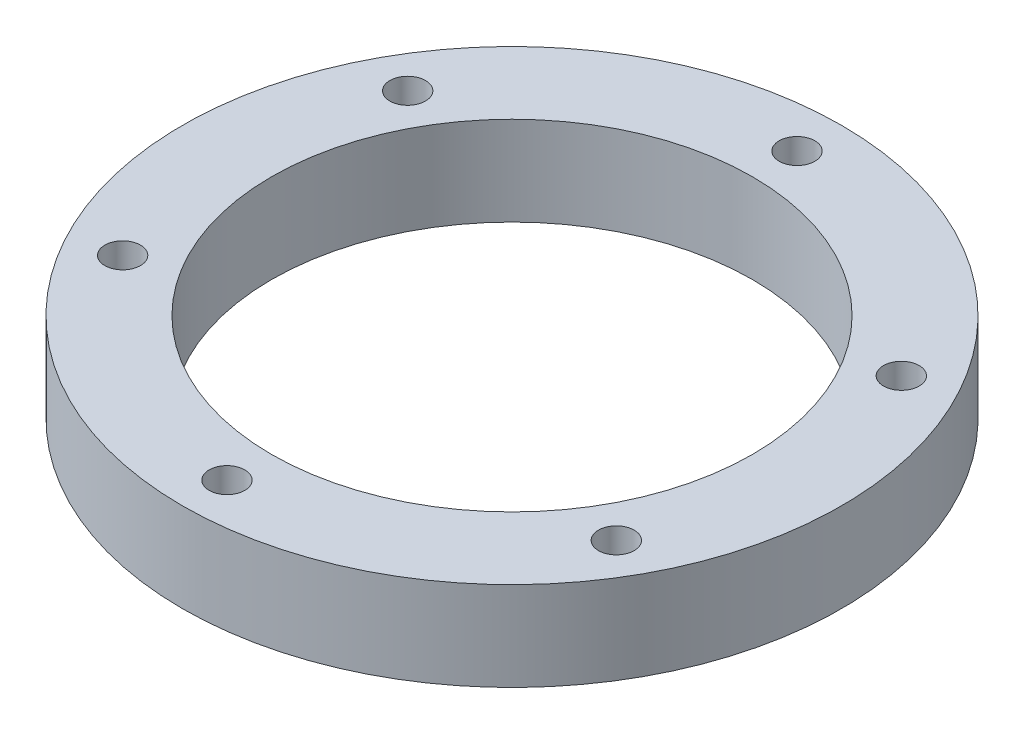
SolidWorks part; units mm, degrees
ref_plane "Front Plane" through (0, 0, 0) normal (0, 0, 1) x (1, 0, 0)
ref_plane "Top Plane" through (0, 0, 0) normal (0, 1, 0) x (1, 0, 0)
ref_plane "Right Plane" through (0, 0, 0) normal (1, 0, 0) x (0, 0, -1)
sketch "Sketch1" plane through (0, 0, 0) normal (0, 1, 0) x (1, 0, 0)
  circle A0 centre (0, 0) radius 45
extrude "Boss-Extrude1" add sketch "Sketch1" along normal blind 10
sketch "Sketch2" plane through (0, 10, 0) normal (0, 1, 0) x (1, 0, 0)
  circle A0 centre (0, 0) radius 37
  circle A1 centre (0, 0) radius 45
  circle A2 centre (0, 0) radius 27
  circle M2 centre (0, 0) radius 45
  dimension "D1" = 10
  dimension "D2" = 90
  dimension "D3" = 74
  dimension "D4" = 54
extrude "Cut-Extrude1" cut sketch "Sketch2" against normal blind 10 contours A2 | A0 M2
sketch "Sketch3" plane through (0, 10, 0) normal (0, 1, 0) x (1, 0, 0)
  line L0 (0, 0) -> (0, 37) construction
  circle A0 centre (0, 0) radius 37 construction
  circle A2 centre (0, 32) radius 2
  circle A3 centre (27.7128, 16) radius 2
  circle A4 centre (27.7128, -16) radius 2
  circle A5 centre (0, -32) radius 2
  circle A6 centre (-27.7128, -16) radius 2
  circle A7 centre (-27.7128, 16) radius 2
  point P20 (0, 0)
  dimension "D1" = 5
  dimension "D2" = 6
extrude "Cut-Extrude2" cut sketch "Sketch3" against normal blind 10
